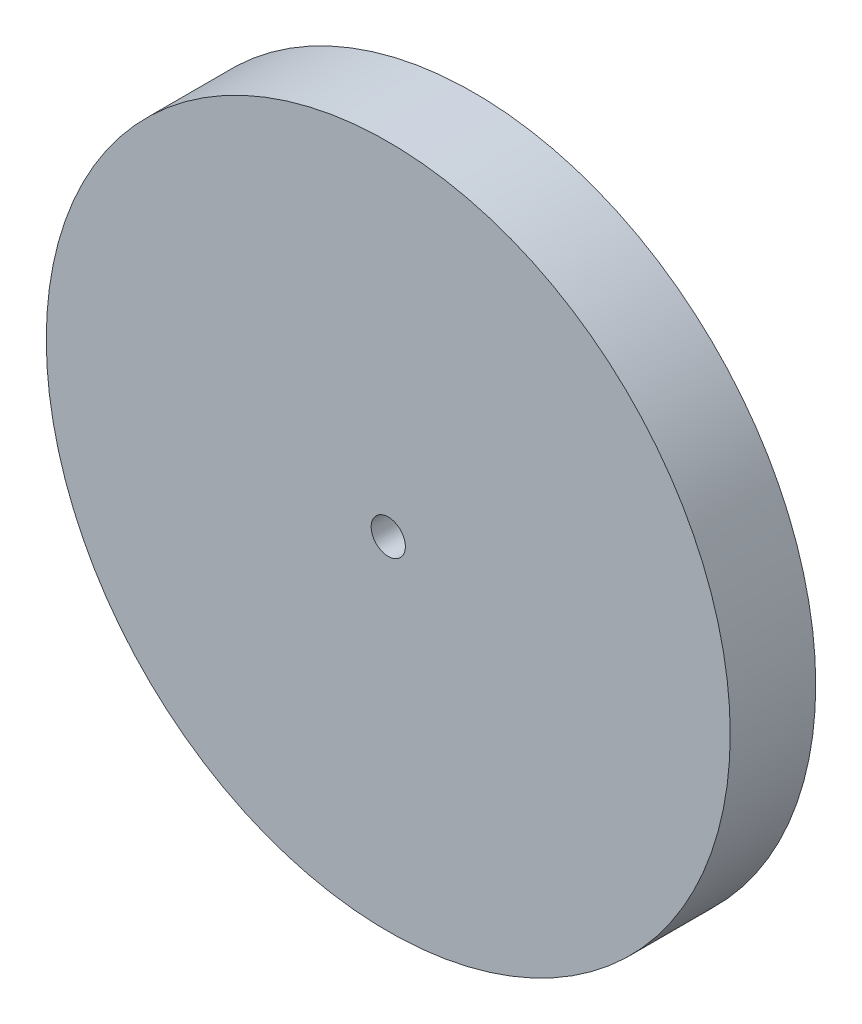
SolidWorks part; units mm, degrees
ref_plane "Front Plane" through (0, 0, 0) normal (0, 0, 1) x (1, 0, 0)
ref_plane "Top Plane" through (0, 0, 0) normal (0, 1, 0) x (1, 0, 0)
ref_plane "Right Plane" through (0, 0, 0) normal (1, 0, 0) x (0, 0, -1)
sketch "Sketch1" plane through (0, 0, 0) normal (0, 0, 1) x (1, 0, 0)
  circle A0 centre (0, -25.4) radius 1.27
  circle A4 centre (0, -25.4) radius 25.4
  dimension "D1" = 2.54
  dimension "D2" = 50.8
extrude "Boss-Extrude1" add sketch "Sketch1" along normal blind 6.35
